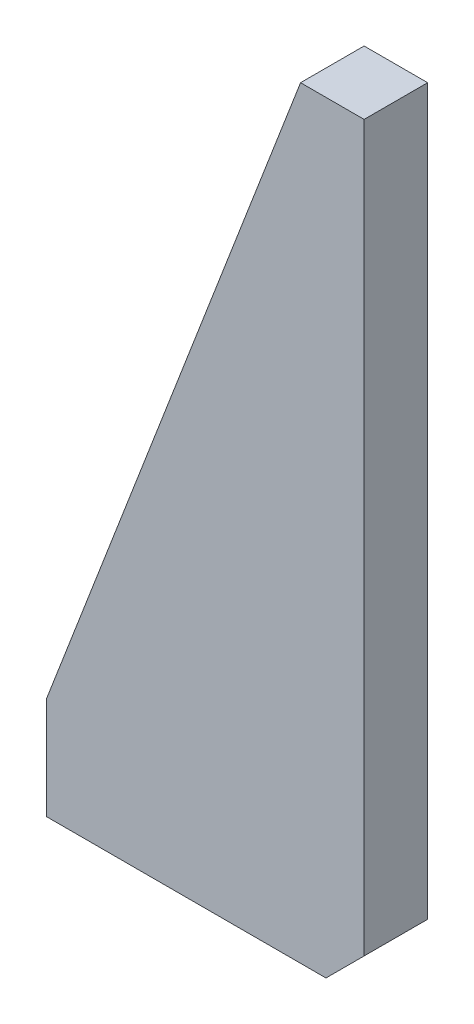
SolidWorks part; units mm, degrees
ref_plane "Спереди" through (0, 0, 0) normal (0, 0, 1) x (1, 0, 0)
ref_plane "Сверху" through (0, 0, 0) normal (0, 1, 0) x (1, 0, 0)
ref_plane "Справа" through (0, 0, 0) normal (1, 0, 0) x (0, 0, -1)
sketch "Эскиз1" plane through (0, 0, 0) normal (0, 0, 1) x (1, 0, 0)
  line L0 (0, 300) -> (-25, 300)
  line L1 (-25, 300) -> (-125, 40)
  line L2 (-125, 40) -> (-125, 0)
  line L3 (-125, 0) -> (0, 0)
  line L4 (0, 0) -> (0, 300)
extrude "Бобышка-Вытянуть1" add sketch "Эскиз1" along normal mid plane 25
chamfer "Фаска1" distance 15 angle 45 1 edges at (0, 0, 0)
